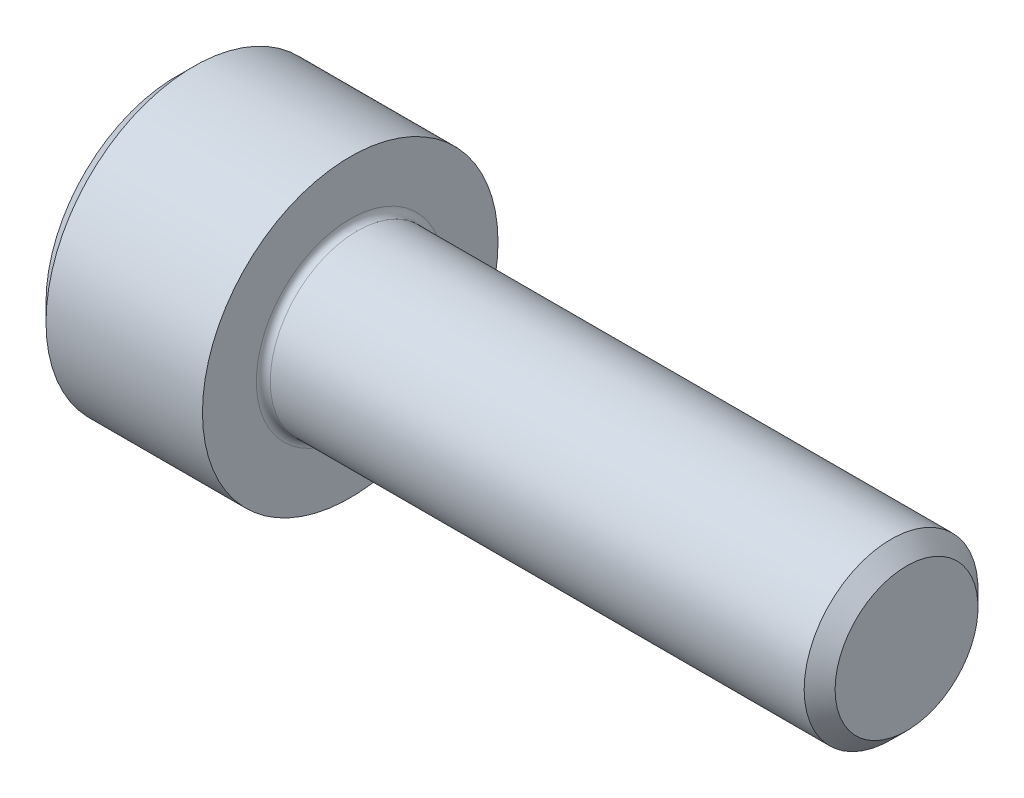
SolidWorks part; units mm, degrees
revolve "Base-Revolve" add sketch "BodySke"
sketch "BodySke" plane through (0, 0, 0) normal (0, 0, 1) x (1, 0, 0)
  line L0 (0, 0) -> (0, 3.75)
  line L1 (0.5, 4.25) -> (5, 4.25)
  line L2 (5, 4.25) -> (5, 2.5)
  line L3 (5, 2.5) -> (20.555, 2.5)
  line L4 (21, 2.055) -> (21, 0)
  line L5 (21, 0) -> (0, 0)
  line L6 (-31.75, 0) -> (127, 0) construction
  line L7 (0, 3.75) -> (0.5, 4.25)
  line L8 (21, 2.055) -> (20.555, 2.5)
  line L9 (0, -3.75) -> (0.5, -4.25) construction
  line L10 (21, -2.055) -> (20.555, -2.5) construction
  line L11 (5.8, 9.525) -> (5.8, 3.175) construction
  line L12 (5, 9.525) -> (5, 3.175) construction
  line L13 (-29, 9.525) -> (-29, 3.175) construction
  dimension "Diameter" = 5
  dimension "Head_ht" = 5
  dimension "Length" = 16
  dimension "Body_ch_ang" = 45
  dimension "Head_dia" = 8.5
  dimension "Head_ch_ang" = 45
  dimension "Minor_dia" = 4.11
  dimension "Advance" = 0.8
  dimension "Thread_nom" = 16
  dimension "Thread_length" = 50
  dimension "Head_ch_ht" = 0.5
cosmetic thread "ThreadCosmetic" [suppressed]
fillet "Fillet1" radius 0.2 1 edges at (5, 0, 2.5)
ref_plane "Plane1" through (0, 0, 0) normal (0, 0, 1) x (1, 0, 0)
ref_plane "Plane2" through (0, 0, 0) normal (0, 1, 0) x (1, 0, 0)
ref_plane "Plane3" through (0, 0, 0) normal (1, 0, 0) x (0, 0, -1)
sketch "Sketch2" plane through (0, 0, 0) normal (0, 0, 1) x (1, 0, 0)
  line L0 (0, 2.042) -> (2.5, 2.042)
  line L1 (2.5, 2.042) -> (3.6789, 0)
  line L2 (-31.75, 0) -> (127, 0) construction
  line L3 (3.6789, 0) -> (0, 0)
  line L4 (0, 0) -> (0, 2.042)
  line L5 (0, 3.75) -> (0, -3.75) construction
  line L6 (0, 0) -> (47.625, 0) construction
  line L7 (5, -4.25) -> (5, 4.25) construction
  dimension "D2" = 60
revolve "Hex-PreBroach" cut sketch "Sketch2" angle 360 about L6
sketch "Sketch3" plane through (0, 0, 0) normal (-1, 0, 0) x (0, 0.5, 0.866)
  line L0 (1.1789, 2.042) -> (-1.1789, 2.042)
  line L1 (-1.1789, 2.042) -> (-2.3579, 0)
  line L2 (1.1789, 2.042) -> (2.3579, 0)
  line L3 (1.1789, -2.042) -> (2.3579, 0)
  line L4 (1.1789, -2.042) -> (-1.1789, -2.042)
  line L5 (-1.1789, -2.042) -> (-2.3579, 0)
extrude "Hex" cut sketch "Sketch3" against normal blind 2.5
sketch "Sketch4" plane through (0, 0, 0) normal (-1, 0, 0) x (0, 0, 1)
  line L0 (0, 0) -> (2.3876, 0)
  line L1 (0, 0) -> (6.1484, 3.5498) construction
  line L2 (0, 0) -> (1.1938, 2.0677)
  line L3 (1.9883, 0.576) -> (2.2704, 0.7389)
  line L4 (1.493, 1.4339) -> (1.7751, 1.5968)
  arc A0 (1.9883, 0.576) -> (1.493, 1.4339) centre (0, 0) ccw
  arc A1 (2.3876, 0) -> (2.2704, 0.7389) centre (0, 0) ccw
  arc A2 (1.1938, 2.0677) -> (1.7751, 1.5968) centre (0, 0) cw
  dimension "D1" = 30
  dimension "D2" = 60
extrude "Spline" [suppressed] cut sketch "Sketch4" against normal blind 2.5
pattern_circular "CirPattern1" [suppressed] count 6 every 60
sketch "Sketch5" plane through (0, 0, 0) normal (0, 0, 1) x (1, 0, 0)
  line L0 (-31.75, 0) -> (127, 0) construction
  line L2 (0, 3.75) -> (0, -3.75) construction
  circle A0 centre (2, 0) radius 0.675
  dimension "Drilled_hole_dia" = 1.35
  dimension "Drilled_hole_loc" = 2
extrude "Hole" [suppressed] cut sketch "Sketch5" against normal through all and the other way through all
pattern_circular "Drilled-4" [suppressed] count 2 every 60
pattern_circular "Drilled-6" [suppressed] count 3 every 60
sketch "ThdSchSke" plane through (0, 0, 0) normal (0, 0, 1) x (1, 0, 0)
  line L0 (5.8, -2.055) -> (5.4884, -2.5)
  line L1 (5.8, -2.055) -> (6.1116, -2.5)
  line L2 (6.1116, -2.5) -> (6.1116, -3.125)
  line L3 (-3.175, 0) -> (5.1513, 0) construction
  line L5 (6.1116, -3.125) -> (5.4884, -3.125)
  line L6 (5.4884, -3.125) -> (5.4884, -2.5)
  line L7 (0, 3.75) -> (0, -3.75) construction
revolve "ThreadSchematic" [suppressed] cut sketch "ThdSchSke" angle 360 about L3
pattern_linear "ThdSchPat" [suppressed]
equation "\"D2@Sketch3\" = \"Hex_size@Sketch3\" / 2"
equation "\"D1@Sketch3\" = \"Hex_size@Sketch3\" / 2"
equation "\"D1@Sketch2\" = \"Hex_size@Sketch3\" / 2"
equation "\"D3@Sketch4\" = \"Spline_p_dim@Sketch4\" / 2"
equation "\"Thread_minor@ThreadCosmetic\"  =  \"Minor_dia@BodySke\""
equation "\"D2@CirPattern1\" = 360 / \"Num_teeth@CirPattern1\""
equation "\"Wall_thickness@Sketch2\" = \"Head_ht@BodySke\" - \"Key_eng@Hex\""
equation "\"Thread_length@ThreadCosmetic\" = ((sgn( (\"Length@BodySke\" - \"Advance@BodySke\" ) - \"Thread_nom@BodySke\" )-1)*( (\"Length@BodySke\" - \"Advance@BodySke\" ) - \"Thread_nom@BodySke\" ))/-2+ \"Thread_nom@BodySke\""
equation "\"Thread_minor@ThdSchSke\" = \"Minor_dia@BodySke\""
equation "\"Diameter@ThdSchSke\" = \"Diameter@BodySke\""
equation "\"Overcut@ThdSchSke\" = \"Diameter@BodySke\" * 1.25"
equation "\"Start@ThdSchSke\" = \"Head_ht@BodySke\" + \"Length@BodySke\" - \"Thread_length@ThreadCosmetic\"  '---Non-countersunk---"
equation "\"Num_threads@ThdSchPat\" = int( \"Thread_length@ThreadCosmetic\" / \"Advance@BodySke\" + 0.999 )  + 1"
equation "\"Advance@ThdSchPat\" = \"Thread_length@ThreadCosmetic\" /  (\"Num_threads@ThdSchPat\" - 1) 'relax it"
equation "\"Num_threads@ThdSchPat\" = \"Num_threads@ThdSchPat\" - sgn( \"Num_threads@ThdSchPat\" - 1) '---chamfered tips only---"
